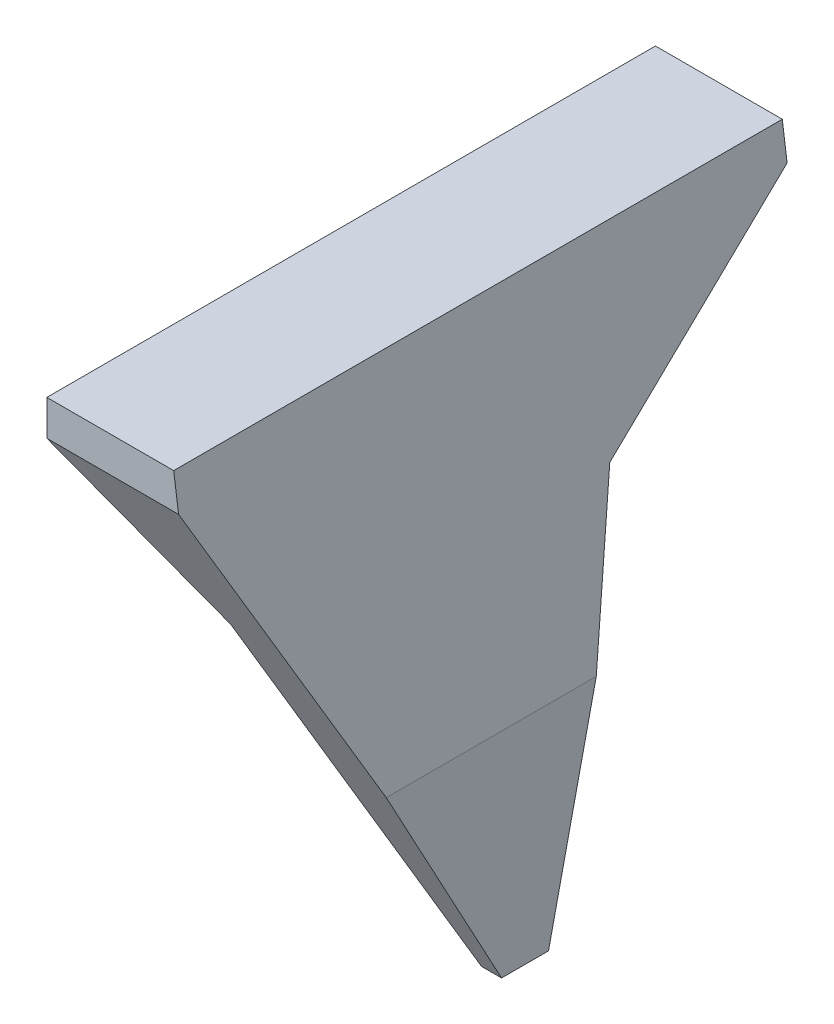
SolidWorks part; units mm, degrees
ref_plane "前视基准面" through (0, 0, 0) normal (0, 0, 1) x (1, 0, 0)
ref_plane "上视基准面" through (0, 0, 0) normal (0, 1, 0) x (1, 0, 0)
ref_plane "右视基准面" through (0, 0, 0) normal (1, 0, 0) x (0, 0, -1)
sketch "草图1" plane through (0, 0, 0) normal (0, 1, 0) x (1, 0, 0)
  line L1 (-10, 35) -> (10, 35)
  line L2 (-10, 35) -> (-10, -35)
  line L3 (-10, -35) -> (10, -35)
  line L4 (10, 35) -> (10, -35)
  line L5 (-10, 35) -> (10, -35) construction
  line L6 (-10, -35) -> (10, 35) construction
  point P0 (0, 0)
  point P6 (0, 0)
  dimension "D1" = 70
  dimension "D2" = 20
extrude "凸台-拉伸1" add sketch "草图1" along normal blind 68
sketch "草图2" plane through (0, 0, 0) normal (0, -1, 0) x (1, 0, 0)
  line L1 (1.8411, 6.3201) -> (-8.5, 6.3201)
  line L2 (1.8411, 6.3201) -> (1.8411, -7.9244)
  line L3 (1.8411, -7.9244) -> (-8.5, -7.9244)
  line L4 (-8.5, 6.3201) -> (-8.5, -7.9244)
  line L5 (1.8411, 6.3201) -> (-8.5, -7.9244) construction
  line L6 (1.8411, -7.9244) -> (-8.5, 6.3201) construction
  point P0 (-3.3295, -0.8022)
extrude "切除-拉伸1" cut sketch "草图2" against normal blind 66.5
sketch "草图3" plane through (-10, 0, 0) normal (-1, 0, 0) x (0, 0, 1)
  line L0 (-35, 68) -> (-35, 63.9236)
  line L1 (-35, 68) -> (-35, 0) construction
  line L2 (-35, 63.9236) -> (-12.229, 46.6695)
  line L3 (-12.229, 46.6695) -> (-2.7013, 4.0152)
  line L4 (-2.7013, 4.0152) -> (2.7013, 4.0152)
  line L5 (2.7013, 4.0152) -> (35, 63.9236)
  line L6 (0, 4.0152) -> (0, 0) construction
  line L7 (-35, 0) -> (35, 0) construction
  line L8 (35, 68) -> (35, 0) construction
  line L9 (35, 63.9236) -> (35, 68)
  line L10 (35, 68) -> (43.7819, 68)
  line L11 (43.7819, 68) -> (43.7819, -5.0435)
  line L12 (43.7819, -5.0435) -> (-39.0899, -5.0435)
  line L13 (-39.0899, -5.0435) -> (-39.0899, 68)
  line L14 (-39.0899, 68) -> (-35, 68)
  line L15 (-35, 63.9236) -> (35, 63.9236) construction
extrude "切除-拉伸2" cut sketch "草图3" against normal blind 28.5 and the other way blind 27
sketch "草图4" plane through (0, 0, -35) normal (0, 0, -1) x (-1, 0, 0)
  line L0 (-4.5886, 68) -> (-10, 28.6103)
  line L1 (-10, 68) -> (10, 68) construction
  line L2 (-4.5886, 80.348) -> (-4.5886, 68) construction
  line L3 (-10, 46.6695) -> (-10, 4.0152) construction
  line L4 (-7.701, 4.0152) -> (-1.8411, 46.6695)
  line L5 (-1.8411, 4.0152) -> (-10, 4.0152) construction
  line L6 (-1.8411, 46.6695) -> (10, 63.9236)
  line L7 (10, 63.9236) -> (16.4632, 63.9236)
  line L8 (16.4632, 63.9236) -> (16.4632, -1.0777)
  line L9 (16.4632, -1.0777) -> (-7.701, -1.0777)
  line L10 (-7.701, -1.0777) -> (-7.701, 4.0152)
  line L11 (-4.5886, 68) -> (-10, 68)
  line L12 (-10, 68) -> (-10, 28.6103)
  point P17 (0, 0)
  line M10 (-10, 63.9236) -> (10, 63.9236)
  line M12 (10, 68) -> (-10, 68)
  line M13 (-10, 68) -> (-10, 63.9236)
extrude "切除-拉伸3" cut sketch "草图4" against normal blind 80.5 and the other way blind 18 contours L12 L0 M10 | L0 M12 M13 M10 | L10 L4 L6 L7 L8 L9
